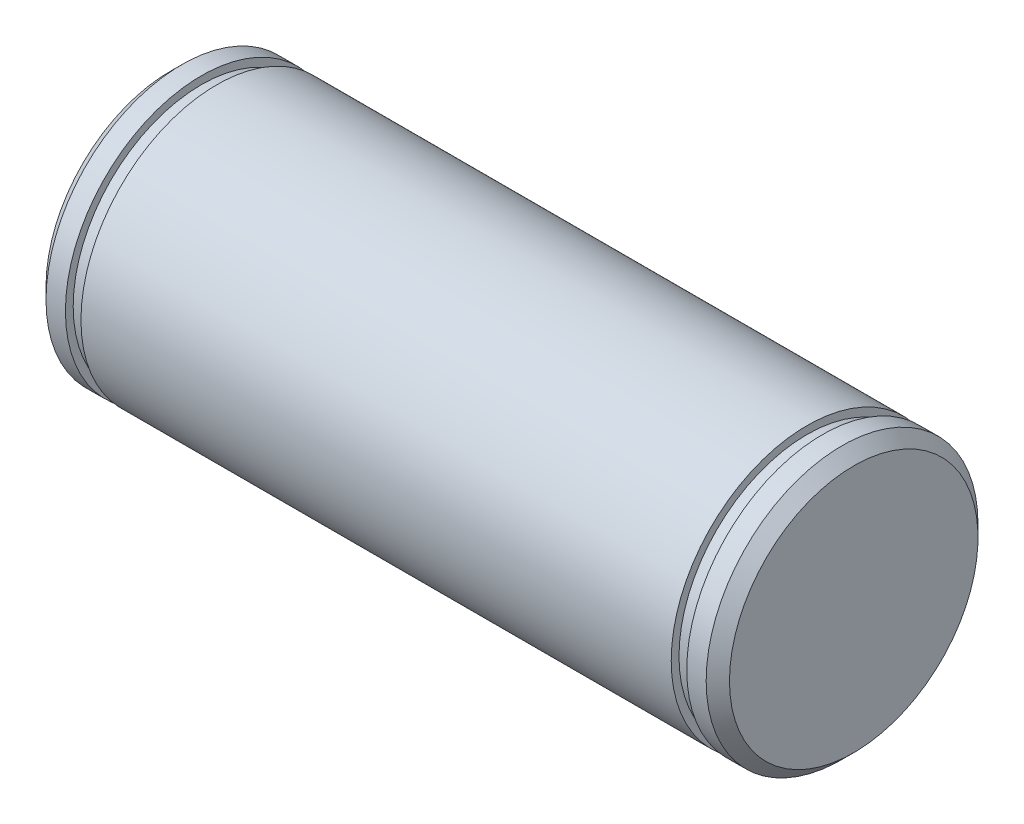
SolidWorks part; units mm, degrees
ref_plane "Front Plane" through (0, 0, 0) normal (0, 0, 1) x (1, 0, 0)
ref_plane "Top Plane" through (0, 0, 0) normal (0, 1, 0) x (1, 0, 0)
ref_plane "Right Plane" through (0, 0, 0) normal (1, 0, 0) x (0, 0, -1)
sketch "Sketch1" plane through (0, 0, 0) normal (0, 0, 1) x (1, 0, 0)
  line L1 (4, 17.5) -> (1.5, 17.5)
  line L4 (6, 16.5) -> (4, 16.5)
  line L8 (1.5, 17.5) -> (0, 16)
  line L10 (1.5, 17.5) -> (4, 17.5)
  line L11 (0, 0) -> (0, 16)
  line L12 (82, 17.5) -> (6, 17.5)
  line L15 (82, 16.5) -> (84, 16.5)
  line L19 (86.5, 17.5) -> (88, 16)
  line L21 (-2, 0) -> (90, 0) construction
  line L22 (86.5, 17.5) -> (84, 17.5)
  line L23 (88, 0) -> (88, 16)
  line L25 (84, 16.5) -> (84, 17.5)
  line L26 (82, 16.5) -> (82, 17.5)
  line L27 (6, 16.5) -> (6, 17.5)
  line L28 (4, 16.5) -> (4, 17.5)
  dimension "D1" = 88
  dimension "D2" = 17.5
  dimension "D3" = 2
  dimension "D4" = 1
  dimension "D5" = 16.5
  dimension "D6" = 1.5
  dimension "D7" = 1.5
  dimension "D9" = 2
  dimension "D10" = 1
  dimension "D11" = 6
  dimension "D12" = 1.5
  dimension "D13" = 45
  dimension "D15" = 76
revolve "Revolve1" add sketch "Sketch1" angle 360 about L21
